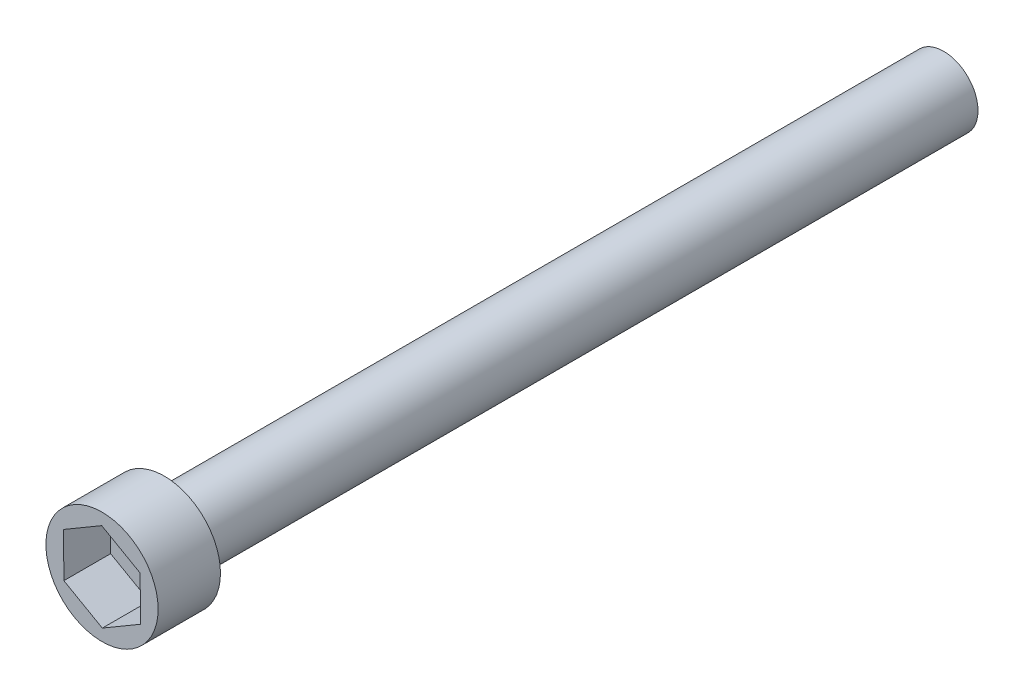
SolidWorks part; units mm, degrees
ref_plane "Front Plane" through (0, 0, 0) normal (0, 0, 1) x (1, 0, 0)
ref_plane "Top Plane" through (0, 0, 0) normal (0, 1, 0) x (1, 0, 0)
ref_plane "Right Plane" through (0, 0, 0) normal (1, 0, 0) x (0, 0, -1)
sketch "Sketch1" plane through (0, 0, 0) normal (0, 0, 1) x (1, 0, 0)
  circle A0 centre (0, 0) radius 1.397
  dimension "D1" = 2.794
extrude "Boss-Extrude1" add sketch "Sketch1" along normal blind 31.75 contours A0
sketch "Sketch2" plane through (0, 0, 31.75) normal (0, 0, 1) x (1, 0, 0)
  circle A0 centre (0, 0) radius 2.286
  dimension "D1" = 4.572
extrude "Boss-Extrude2" add sketch "Sketch2" along normal blind 2.54
sketch "Sketch4" plane through (0, 0, 34.29) normal (0, 0, 1) x (1, 0, 0)
  line L1 (1.5664, -0.8899) -> (1.5539, 0.9116)
  line L2 (1.5539, 0.9116) -> (-0.0125, 1.8015)
  line L3 (-0.0125, 1.8015) -> (-1.5664, 0.8899)
  line L4 (-1.5664, 0.8899) -> (-1.5539, -0.9116)
  line L5 (-1.5539, -0.9116) -> (0.0125, -1.8015)
  line L6 (0.0125, -1.8015) -> (1.5664, -0.8899)
  circle A0 centre (0, 0) radius 1.5602 construction
extrude "Cut-Extrude1" cut sketch "Sketch4" against normal blind 1.905
